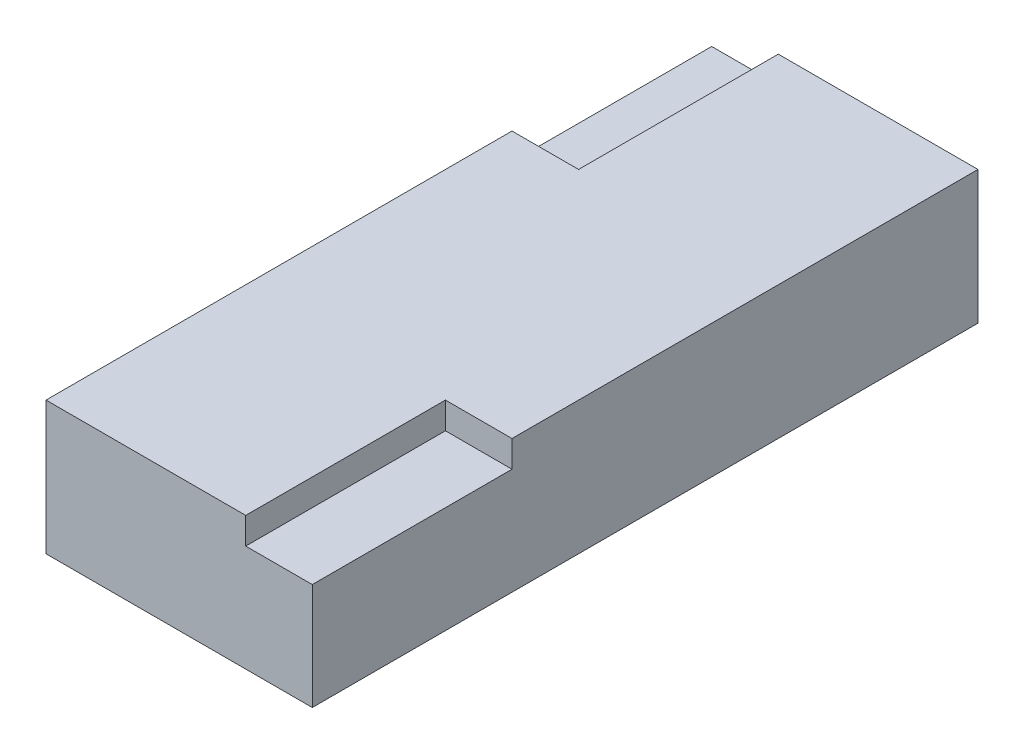
SolidWorks part; units mm, degrees
ref_plane "Front Plane" through (0, 0, 0) normal (0, 0, 1) x (1, 0, 0)
ref_plane "Top Plane" through (0, 0, 0) normal (0, 1, 0) x (1, 0, 0)
ref_plane "Right Plane" through (0, 0, 0) normal (1, 0, 0) x (0, 0, -1)
sketch "Sketch1" plane through (0, 0, 0) normal (0, 1, 0) x (1, 0, 0)
  line L1 (0, 0) -> (20, 0)
  line L2 (0, 0) -> (0, 50)
  line L3 (0, 50) -> (20, 50)
  line L4 (20, 0) -> (20, 50)
  dimension "D1" = 50
  dimension "D2" = 20
extrude "Boss-Extrude1" add sketch "Sketch1" along normal blind 10
sketch "Sketch2" plane through (0, 10, 0) normal (0, 1, 0) x (1, 0, 0)
  line L1 (20, 0) -> (15, 0)
  line L2 (20, 0) -> (20, 15)
  line L3 (20, 15) -> (15, 15)
  line L4 (15, 0) -> (15, 15)
  line L5 (0, 50) -> (5, 50)
  line L6 (0, 50) -> (0, 35)
  line L7 (0, 35) -> (5, 35)
  line L8 (5, 50) -> (5, 35)
  dimension "D1" = 15
  dimension "D2" = 5
  dimension "D3" = 15
  dimension "D4" = 5
extrude "Cut-Extrude1" cut sketch "Sketch2" against normal blind 2
equation "\"D3@Sketch2\"=\"D1@Sketch2\""
equation "\"D4@Sketch2\"=\"D2@Sketch2\""
